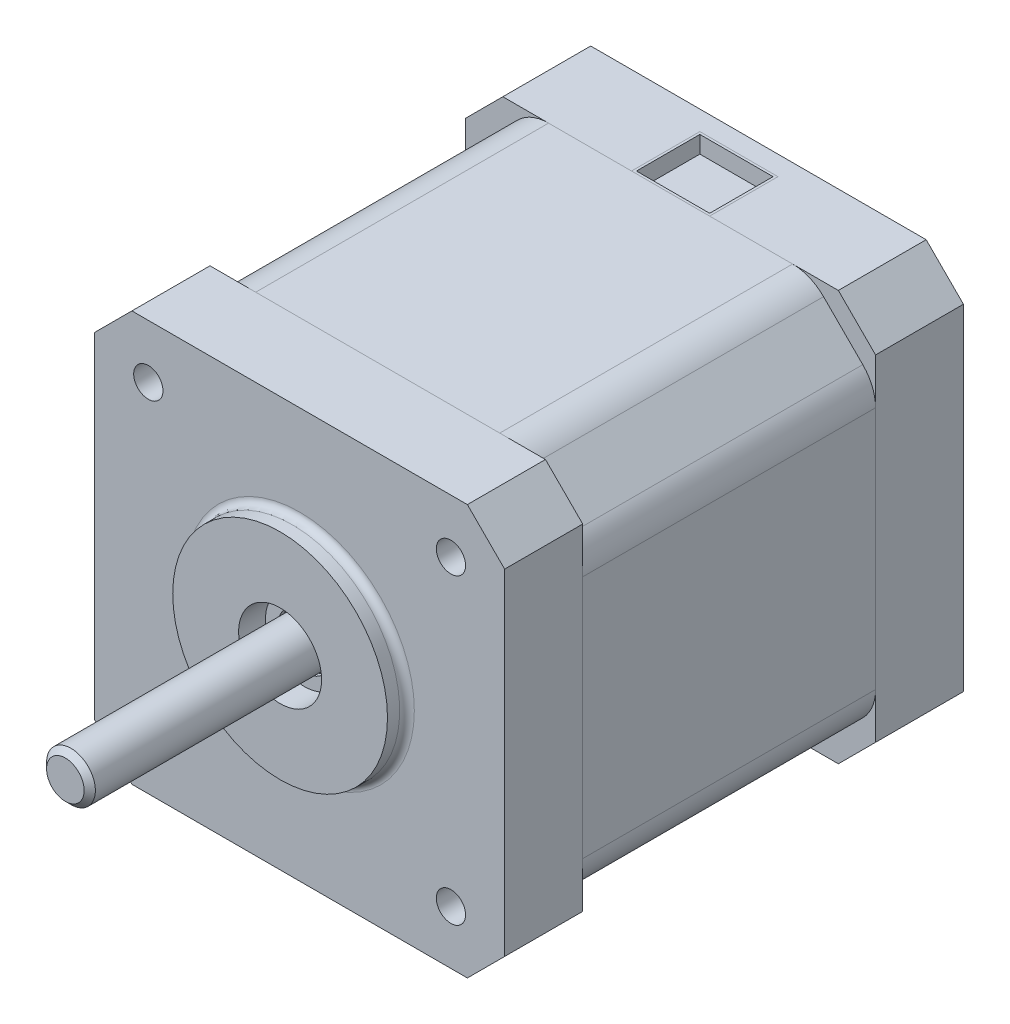
SolidWorks part; units mm, degrees
other "ŞAFT"
other "ARKA"
other "ORTA"
other "ÖN"
other "KABLO"
ref_plane "Front Plane" through (0, 0, 0) normal (0, 0, 1) x (1, 0, 0)
ref_plane "Top Plane" through (0, 0, 0) normal (0, 1, 0) x (1, 0, 0)
ref_plane "Right Plane" through (0, 0, 0) normal (1, 0, 0) x (0, 0, -1)
sketch "Sketch1" plane through (0, 0, 0) normal (0, 0, 1) x (1, 0, 0)
  line L0 (-15.5, 15.5) -> (15.5, 15.5) construction
  line L1 (17.1838, 21) -> (-17.1838, 21)
  line L2 (21, 17.1838) -> (21, -17.1838)
  line L3 (17.1838, -21) -> (-17.1838, -21)
  line L4 (-21, 17.1838) -> (-21, -17.1838)
  line L5 (19.0919, 19.0919) -> (-19.0919, -19.0919) construction
  line L6 (19.0919, -19.0919) -> (-19.0919, 19.0919) construction
  line L7 (15.5, 15.5) -> (15.5, -15.5) construction
  line L8 (15.5, -15.5) -> (-15.5, -15.5) construction
  line L9 (-15.5, -15.5) -> (-15.5, 15.5) construction
  line L10 (17.1838, 21) -> (21, 17.1838)
  line L11 (21, 17.1838) -> (21, 21) construction
  line L12 (21, 21) -> (17.1838, 21) construction
  line L13 (19.0919, 19.0919) -> (21, 21) construction
  line L14 (19.0919, 19.0919) -> (-19.0919, 19.0919) construction
  line L15 (-19.0919, 19.0919) -> (-19.0919, -19.0919) construction
  line L16 (-19.0919, -19.0919) -> (19.0919, -19.0919) construction
  line L17 (19.0919, -19.0919) -> (19.0919, 19.0919) construction
  line L18 (21, -17.1838) -> (17.1838, -21)
  line L19 (-17.1838, -21) -> (-21, -17.1838)
  line L20 (-21, 17.1838) -> (-17.1838, 21)
  line L21 (-19.0919, -19.0919) -> (-21, -21) construction
  line L22 (19.0919, -19.0919) -> (21, -21) construction
  line L23 (-19.0919, 19.0919) -> (-21, 21) construction
  line L24 (21, -17.1838) -> (21, -21) construction
  line L25 (21, -21) -> (17.1838, -21) construction
  line L26 (-17.1838, -21) -> (-21, -21) construction
  line L27 (-21, -21) -> (-21, -17.1838) construction
  line L28 (-21, 17.1838) -> (-21, 21) construction
  line L29 (-21, 21) -> (-17.1838, 21) construction
  circle A0 centre (-15.5, 15.5) radius 1.5 construction
  circle A1 centre (15.5, 15.5) radius 1.5 construction
  circle A2 centre (-15.5, -15.5) radius 1.5 construction
  circle A3 centre (15.5, -15.5) radius 1.5 construction
  point P0 (0, 0)
  dimension "D2" = 3
  dimension "D1" = 42
  dimension "D3" = 31
  dimension "D4" = 54
extrude "Boss-Extrude1" add sketch "Sketch1" against normal blind 8
sketch "Sketch3" plane through (0, 0, -8) normal (0, 0, -1) x (-1, 0, 0)
  line L0 (-19.6881, 15.6673) -> (-15.6673, 19.6881)
  line L1 (15.6673, 19.6881) -> (19.6881, 15.6673)
  line L2 (19.6881, -15.6673) -> (15.6673, -19.6881)
  line L3 (-15.6673, -19.6881) -> (-19.6881, -15.6673)
  line L4 (0, 0) -> (-17.6777, -17.6777) construction
  line L5 (0, 0) -> (17.6777, 17.6777) construction
  line L6 (-17.6777, 17.6777) -> (0, 0) construction
  line L7 (0, 0) -> (17.6777, -17.6777) construction
  line L8 (-17.1838, 21) -> (-21, 17.1838)
  line L9 (-21, 17.1838) -> (-21, -17.1838)
  line L10 (-21, -17.1838) -> (-17.1838, -21)
  line L11 (-17.1838, -21) -> (17.1838, -21)
  line L12 (17.1838, -21) -> (21, -17.1838)
  line L13 (21, -17.1838) -> (21, 17.1838)
  line L14 (21, 17.1838) -> (17.1838, 21)
  line L15 (17.1838, 21) -> (-17.1838, 21)
  line L16 (-17.6777, -17.6777) -> (-19.0919, -19.0919) construction
  line L17 (-21, 12.5) -> (-21, -12.5)
  line L18 (-17.1838, -21) -> (-21, -17.1838) construction
  line L19 (-12.5, -21) -> (12.5, -21)
  line L21 (21, -12.5) -> (21, 12.5)
  line L23 (12.5, 21) -> (-12.5, 21)
  arc A0 (-19.6881, -15.6673) -> (-21, -12.5) centre (-16.5208, -12.5) cw
  arc A1 (-15.6673, -19.6881) -> (-12.5, -21) centre (-12.5, -16.5208) ccw
  arc A2 (15.6673, -19.6881) -> (12.5, -21) centre (12.5, -16.5208) cw
  arc A3 (19.6881, -15.6673) -> (21, -12.5) centre (16.5208, -12.5) ccw
  arc A4 (19.6881, 15.6673) -> (21, 12.5) centre (16.5208, 12.5) cw
  arc A5 (15.6673, 19.6881) -> (12.5, 21) centre (12.5, 16.5208) ccw
  arc A6 (-15.6673, 19.6881) -> (-12.5, 21) centre (-12.5, 16.5208) cw
  arc A7 (-19.6881, 15.6673) -> (-21, 12.5) centre (-16.5208, 12.5) ccw
  dimension "D3" = 25
  dimension "D2" = 50
  dimension "D1" = 0
extrude "Boss-Extrude2" add sketch "Sketch3" along normal blind 30 separate body
sketch "Sketch4" plane through (0, 0, -38) normal (0, 0, -1) x (-1, 0, 0)
  line L8 (-17.1838, 21) -> (-21, 17.1838)
  line L9 (-21, 17.1838) -> (-21, -17.1838)
  line L10 (-21, -17.1838) -> (-17.1838, -21)
  line L11 (-17.1838, -21) -> (17.1838, -21)
  line L12 (17.1838, -21) -> (21, -17.1838)
  line L13 (21, -17.1838) -> (21, 17.1838)
  line L14 (21, 17.1838) -> (17.1838, 21)
  line L15 (17.1838, 21) -> (-17.1838, 21)
  line L16 (-17.1838, 21) -> (-21, 17.1838)
  line L17 (-21, 17.1838) -> (-21, -17.1838)
  line L18 (-21, -17.1838) -> (-17.1838, -21)
  line L19 (-17.1838, -21) -> (17.1838, -21)
  line L20 (17.1838, -21) -> (21, -17.1838)
  line L21 (21, -17.1838) -> (21, 17.1838)
  line L22 (21, 17.1838) -> (17.1838, 21)
  line L23 (17.1838, 21) -> (-17.1838, 21)
  dimension "D1" = 0
extrude "Boss-Extrude3" add sketch "Sketch4" along normal blind 9 separate body
sketch "Sketch5" plane through (0, 0, 0) normal (0, 0, 1) x (1, 0, 0)
  circle A0 centre (-15.5, 15.5) radius 1.5 construction
  circle A1 centre (15.5, 15.5) radius 1.5 construction
  circle A2 centre (15.5, -15.5) radius 1.5 construction
  circle A3 centre (-15.5, -15.5) radius 1.5 construction
  circle A4 centre (-15.5, 15.5) radius 1.5
  circle A5 centre (15.5, 15.5) radius 1.5
  circle A6 centre (15.5, -15.5) radius 1.5
  circle A7 centre (-15.5, -15.5) radius 1.5
extrude "Cut-Extrude1" cut sketch "Sketch5" against normal blind 4.5
sketch "Sketch6" plane through (0, 0, 0) normal (0, 0, 1) x (1, 0, 0)
  circle A0 centre (0, 0) radius 11
  dimension "D1" = 22
extrude "Boss-Extrude4" add sketch "Sketch6" along normal blind 2
sketch "Sketch9" plane through (0, 0, 2) normal (0, 0, 1) x (1, 0, 0)
  circle A0 centre (0, 0) radius 4.25
  dimension "D1" = 8.5
extrude "Cut-Extrude2" cut sketch "Sketch9" against normal blind 3
sketch "Sketch8" plane through (0, 0, -1) normal (0, 0, 1) x (1, 0, 0)
  circle A0 centre (0, 0) radius 2.5
  dimension "D1" = 5
extrude "Boss-Extrude5" add sketch "Sketch8" along normal blind 25 separate body
sketch "Sketch11" plane through (0, 0, -1) normal (0, 0, 1) x (1, 0, 0)
  circle A2 centre (0, 0) radius 4
  circle A3 centre (0, 0) radius 4.25 construction
  circle A4 centre (0, 0) radius 4.25 construction
  circle A5 centre (0, 0) radius 2.75
  dimension "D2" = 5.5
  dimension "D1" = 0.25
extrude "Boss-Extrude6" add sketch "Sketch11" along normal blind 0.5
fillet "Fillet1" radius 0.75 1 edges at (-11, 0, 0)
sketch "Sketch12" plane through (0, 0, 0) normal (1, 0, 0) x (0, 0, -1)
  line L0 (-24, 1.925) -> (-23.425, 2.5)
  line L1 (-24, 2.5) -> (-24, -2.5) construction
  line L2 (1, 2.5) -> (-24, 2.5) construction
  line L3 (-23.425, 2.5) -> (-23.425, 1.925) construction
  line L4 (-23.425, 1.925) -> (-24, 1.925) construction
  line L5 (-24, 1.925) -> (-24, 2.5)
  line L6 (-24, 2.5) -> (-23.425, 2.5)
  line L7 (-24, 0) -> (0, 0) construction
  dimension "D1" = 3.85
revolve "Cut-Revolve1" cut sketch "Sketch12" angle 360 about L7
sketch "Sketch13" plane through (0, 21, 0) normal (0, 1, 0) x (1, 0, 0)
  line L0 (0, 45) -> (0, 38) construction
  line L2 (-12.5, 38) -> (12.5, 38) construction
  line L3 (0, 45) -> (0, 47) construction
  line L4 (-4, 38) -> (4, 38)
  line L5 (-4, 38) -> (-4, 45)
  line L6 (-4, 45) -> (4, 45)
  line L7 (4, 38) -> (4, 45)
  line L8 (-17.1838, 47) -> (17.1838, 47) construction
  dimension "D1" = 2
  dimension "D2" = 8
extrude "Cut-Extrude3" cut sketch "Sketch13" against normal blind 2
sketch "Sketch14" plane through (0, 19, 0) normal (0, 1, 0) x (1, 0, 0)
  line L4 (-4, 45) -> (-4, 38)
  line L5 (-4, 38) -> (4, 38)
  line L6 (4, 38) -> (4, 45)
  line L7 (4, 45) -> (-4, 45)
  line L8 (-4, 45) -> (-4, 38)
  line L9 (-4, 38) -> (4, 38)
  line L10 (4, 38) -> (4, 45)
  line L11 (4, 45) -> (-4, 45)
  dimension "D1" = 0
extrude "Boss-Extrude7" add sketch "Sketch14" along normal blind 0.25 separate body
sketch "Sketch15" plane through (0, 19.25, 0) normal (0, 1, 0) x (1, 0, 0)
  line L0 (3.75, 38.25) -> (3.75, 44.75)
  line L1 (3.75, 44.75) -> (-3.75, 44.75)
  line L2 (-3.75, 44.75) -> (-3.75, 38.25)
  line L3 (-3.75, 38.25) -> (3.75, 38.25)
  line L4 (4, 45) -> (-4, 45)
  line L5 (-4, 45) -> (-4, 38)
  line L6 (-4, 38) -> (4, 38)
  line L7 (4, 38) -> (4, 45)
  line L8 (4, 45) -> (-4, 45)
  line L9 (-4, 45) -> (-4, 38)
  line L10 (-4, 38) -> (4, 38)
  line L11 (4, 38) -> (4, 45)
  dimension "D1" = 0
  dimension "D2" = 0.25
extrude "Boss-Extrude8" add sketch "Sketch15" along normal up to surface (1.75 mm away) up to face at (0, 21, -42)
